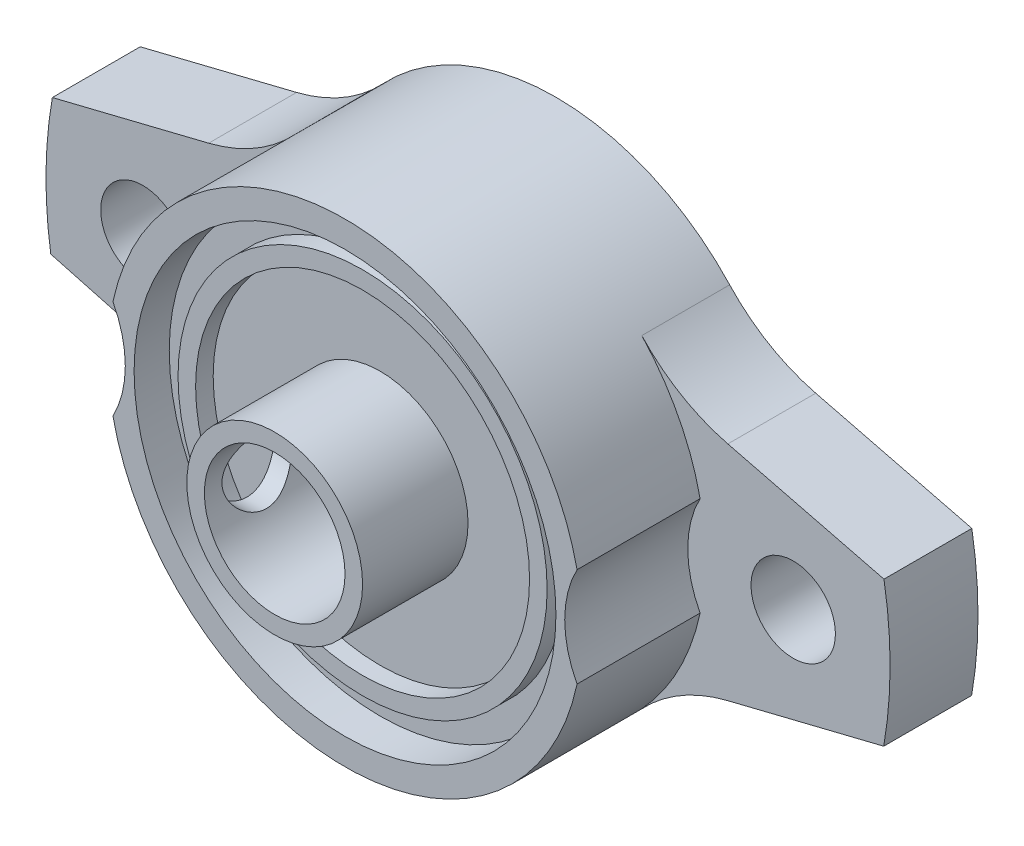
SolidWorks part; units mm, degrees
ref_plane "Front" through (0, 0, 0) normal (0, 0, 1) x (1, 0, 0)
ref_plane "Top" through (0, 0, 0) normal (0, 1, 0) x (1, 0, 0)
ref_plane "Right" through (0, 0, 0) normal (1, 0, 0) x (0, 0, -1)
sketch "草图1" plane through (0, 0, 0) normal (0, 0, 1) x (1, 0, 0)
  line L0 (-23.6505, 4.1558) -> (-14.7553, 6.3539)
  line L1 (14.7812, 6.304) -> (23.6632, 4.083)
  line L7 (-23.7407, -3.6053) -> (-14.9482, -5.9736)
  line L8 (14.7553, -6.3539) -> (23.6505, -4.1558)
  circle A1 centre (18.5, 0) radius 2.4
  circle A2 centre (-18.5, 0) radius 2.4
  arc A3 (9.8849, 9.1945) -> (-9.8545, 9.227) centre (0, 0) ccw
  arc A4 (-23.6505, 4.1558) -> (-23.7407, -3.6053) centre (0, 0) ccw
  arc A5 (23.6505, -4.1558) -> (23.6632, 4.083) centre (0, 0) ccw
  arc A6 (-10.0814, -8.9786) -> (9.8545, -9.227) centre (0, 0) ccw
  arc A7 (-9.8545, 9.227) -> (-14.7553, 6.3539) centre (-17.1542, 16.0619) cw
  arc A8 (-10.0814, -8.9786) -> (-14.9482, -5.9736) centre (-17.549, -15.6295) ccw
  arc A9 (14.7553, -6.3539) -> (9.8545, -9.227) centre (17.1542, -16.0619) ccw
  arc A10 (14.7812, 6.304) -> (9.8849, 9.1945) centre (17.207, 16.0053) cw
  point P18 (-11.6214, -6.8697)
  dimension "D1" = 10
  dimension "D2" = 10
  dimension "D3" = 10
  dimension "D4" = 10
extrude "凸台-拉伸1" add sketch "草图1" along normal blind 5
sketch "草图2" plane through (0, 0, 5) normal (0, 0, 1) x (1, 0, 0)
  circle A0 centre (0, 0) radius 13.5
extrude "凸台-拉伸2" add sketch "草图2" along normal blind 5 contours A0
sketch "草图3" plane through (0, 0, 10) normal (0, 0, 1) x (1, 0, 0)
  circle A0 centre (0, 0) radius 13.5
  circle A1 centre (0, 0) radius 12
extrude "凸台-拉伸3" add sketch "草图3" along normal blind 2
sketch "草图4" plane through (0, 0, 10) normal (0, 0, 1) x (1, 0, 0)
  circle A0 centre (0, 0) radius 4
  circle A1 centre (0, 0) radius 5
extrude "凸台-拉伸4" add sketch "草图4" along normal blind 6
sketch "草图5" plane through (0, 0, 5) normal (0, 0, 1) x (1, 0, 0)
  circle A0 centre (-18.5, 0) radius 6
  circle A1 centre (18.5, 0) radius 6
extrude "切除-拉伸1" cut sketch "草图5" along normal blind 7
sketch "草图6" plane through (0, 0, 10) normal (0, 0, 1) x (1, 0, 0)
  circle A0 centre (0, 0) radius 4
extrude "切除-拉伸2" cut sketch "草图6" against normal blind 13
sketch "草图7" plane through (0, 0, 10) normal (0, 0, 1) x (1, 0, 0)
  circle A0 centre (0, 0) radius 10.5
  circle A1 centre (0, 0) radius 9.5
extrude "凸台-拉伸5" add sketch "草图7" along normal blind 1
ref_plane "基准面1" through (-5, 0, 0) normal (-1, 0, 0) x (0, 0, 1)
sketch "草图8" plane through (-5, 0, 0) normal (-1, 0, 0) x (0, 0, 1)
  circle A0 centre (13, 0) radius 2
  point P2 (13, 0)
extrude "切除-拉伸3" cut sketch "草图8" against normal blind 3
